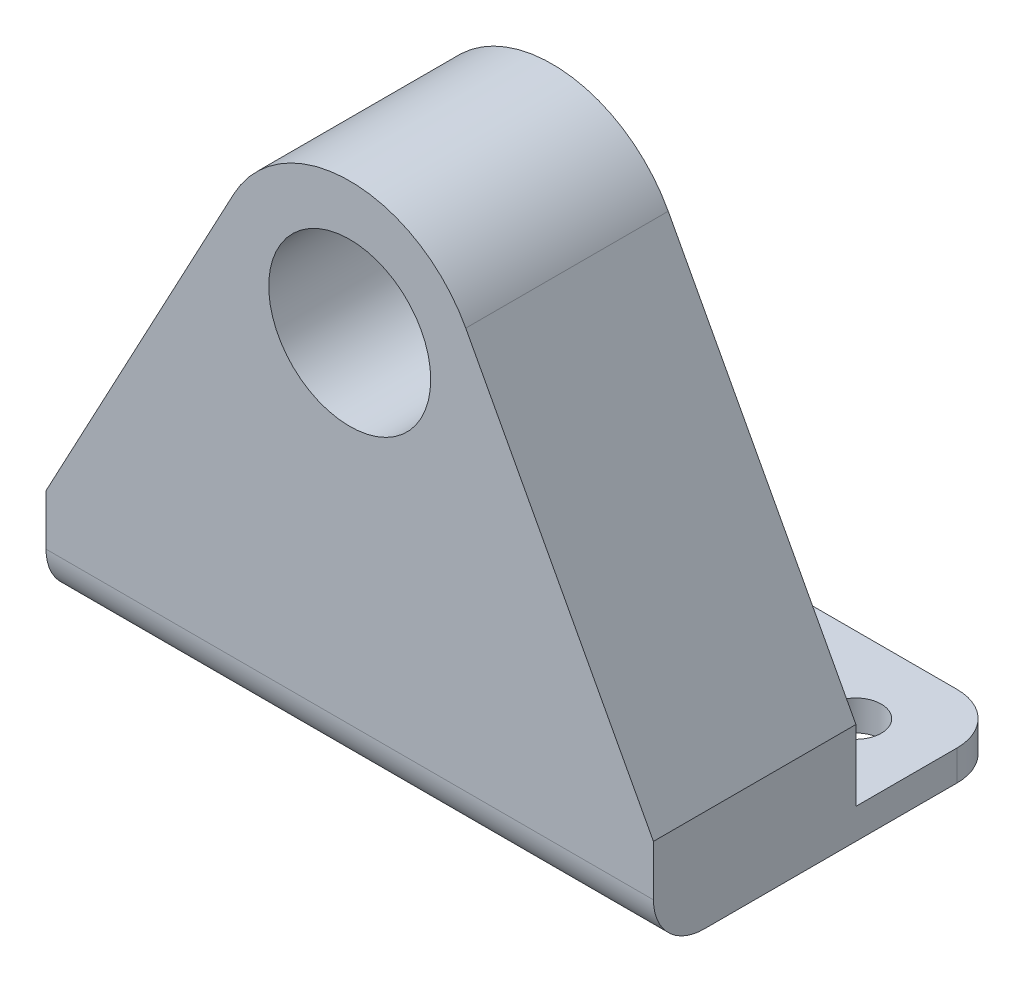
SolidWorks part; units mm, degrees
ref_plane "Front Plane" through (0, 0, 0) normal (0, 0, 1) x (1, 0, 0)
ref_plane "Top Plane" through (0, 0, 0) normal (0, 1, 0) x (1, 0, 0)
ref_plane "Right Plane" through (0, 0, 0) normal (1, 0, 0) x (0, 0, -1)
sketch "Sketch1" plane through (0, 0, 0) normal (0, 0, 1) x (1, 0, 0)
  line L0 (0, 0) -> (0, -28.5) construction
  line L1 (-30, -28.5) -> (30, -28.5) construction
  line L2 (30, -28.5) -> (30, -38.5)
  line L3 (30, -38.5) -> (-30, -38.5)
  line L4 (-30, -38.5) -> (-30, -28.5)
  line L5 (-30, -28.5) -> (-11.4614, 6.1348)
  line L7 (30, -28.5) -> (11.4614, 6.1348)
  circle A0 centre (0, 0) radius 8
  arc A1 (11.4614, 6.1348) -> (-11.4614, 6.1348) centre (0, 0) ccw
  point P8 (0, -28.5)
  dimension "D1" = 16
  dimension "D2" = 26
  dimension "D3" = 28.5
  dimension "D4" = 60
  dimension "D5" = 10
extrude "Boss-Extrude1" add sketch "Sketch1" along normal blind 20
sketch "Sketch2" plane through (0, 0, 0) normal (0, 0, -1) x (-1, 0, 0)
  line L0 (30, -28.5) -> (30, -38.5) construction
  line L1 (-30, -38.5) -> (30, -38.5)
  line L2 (-30, -38.5) -> (-30, -35.5)
  line L3 (-30, -35.5) -> (30, -35.5)
  line L4 (30, -38.5) -> (30, -35.5)
  dimension "D1" = 3
extrude "Boss-Extrude2" add sketch "Sketch2" along normal blind 15
sketch "Sketch3" plane through (0, -38.5, 0) normal (0, -1, 0) x (1, 0, 0)
  line L0 (-30, 0) -> (30, 0) construction
  line L1 (-30, 20) -> (-30, -15) construction
  line L2 (30, 20) -> (30, -15) construction
  line L3 (-22.5, 0) -> (-22.5, -15) construction
  line L4 (30, -15) -> (-30, -15) construction
  line L5 (22.5, 0) -> (22.5, -15) construction
  circle A0 centre (22.5, -7.5) radius 2.5
  circle A1 centre (-22.5, -7.5) radius 2.5
  point P16 (0, 0)
  point P17 (0, 0)
  dimension "D3" = 5
  dimension "D4" = 5
  dimension "D1" = 7.5
  dimension "D2" = 7.5
  dimension "D5" = 15
extrude "Cut-Extrude1" cut sketch "Sketch3" against normal blind 20
fillet "Fillet1" radius 5 3 edges at (30, -37, -15) (-30, -37, -15) (0, -38.5, 20)
sketch "Sketch4" plane through (0, 0, 20) normal (0, 0, 1) x (1, 0, 0)
  line L0 (-30, -28.5) -> (30, -28.5) construction
  line L1 (24.3288, -28.5) -> (11.111, -3.8058) construction
  line L2 (30, -28.5) -> (11.4614, 6.1348) construction
  dimension "D1" = 28.0091
  dimension "D2" = 5
